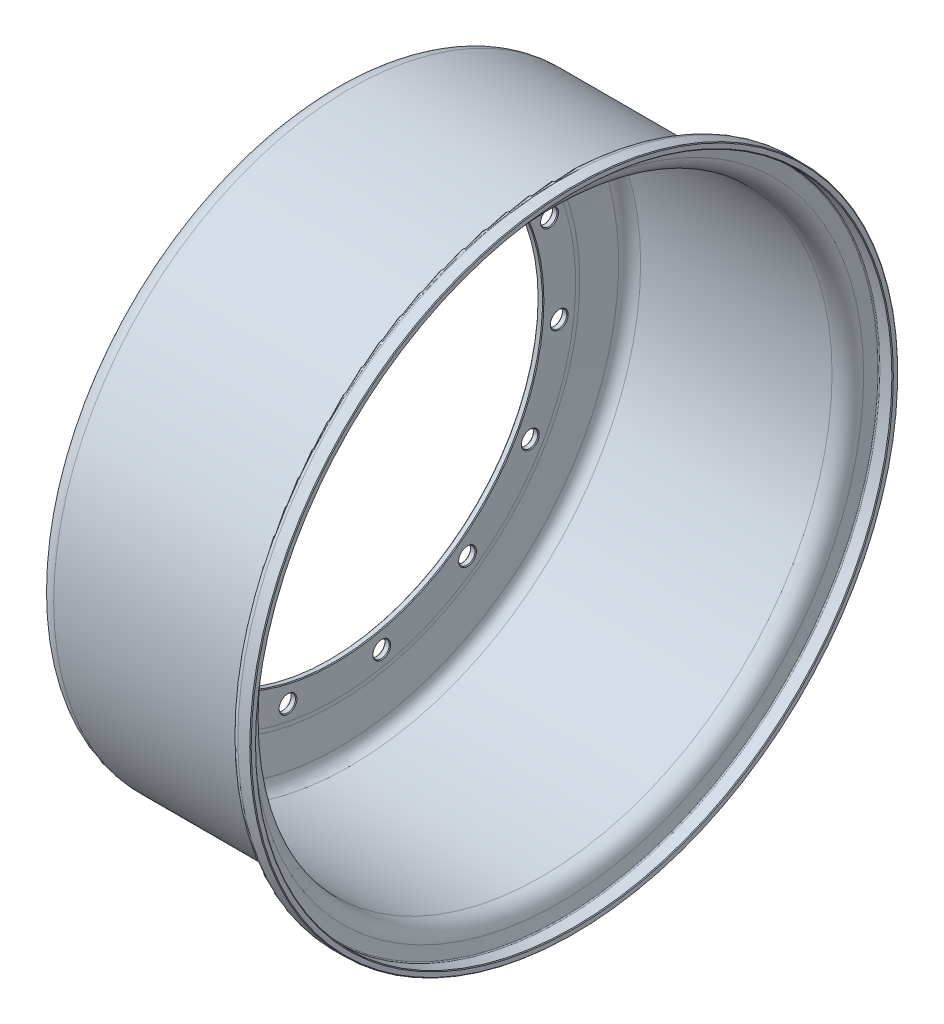
SolidWorks part; units mm, degrees
material "6061-T6 (SS)"
ref_plane "Front Plane" through (0, 0, 0) normal (0, 0, 1) x (1, 0, 0)
ref_plane "Top Plane" through (0, 0, 0) normal (0, 1, 0) x (1, 0, 0)
ref_plane "Right Plane" through (0, 0, 0) normal (1, 0, 0) x (0, 0, -1)
ref_axis "Axis1" through (-6.731, 0, 0) along (1, 0, 0)
sketch "Sketch1" plane through (0, 0, 0) normal (0, 0, 1) x (1, 0, 0)
  line L0 (0, -97.7897) -> (0, 97.7897) construction
  line L1 (0, 114.3) -> (0, 132.1206)
  line L2 (0.1187, 134.574) -> (2.0071, 154.0431)
  line L3 (3.175, 114.3) -> (3.175, 132.1206)
  line L4 (11.4879, 162.6489) -> (116.5449, 162.6489)
  line L5 (122.8075, 167.9487) -> (123.9262, 174.6196)
  line L6 (127.6838, 177.7995) -> (134.6206, 177.7995)
  line L7 (3.2789, 134.2674) -> (5.1673, 153.7366)
  line L8 (11.4879, 159.4739) -> (116.5449, 159.4739)
  line L9 (125.9388, 167.4236) -> (127.0575, 174.0945)
  line L10 (127.6838, 174.6245) -> (134.6206, 174.6245)
  line L11 (134.6206, 177.7995) -> (134.6206, 174.6245)
  line L12 (0, 114.3) -> (3.175, 114.3)
  arc A0 (0, 132.1206) -> (0.1187, 134.574) centre (25.4122, 132.1206) cw
  arc A1 (2.0071, 154.0431) -> (11.4879, 162.6489) centre (11.4879, 153.1235) cw
  arc A2 (116.5449, 162.6489) -> (122.8075, 167.9487) centre (116.5449, 168.999) ccw
  arc A3 (123.9262, 174.6196) -> (127.6838, 177.7995) centre (127.6838, 173.9894) cw
  arc A4 (3.175, 132.1206) -> (3.2789, 134.2674) centre (25.4122, 132.1206) cw
  arc A5 (5.1673, 153.7366) -> (11.4879, 159.4739) centre (11.4879, 153.1235) cw
  arc A6 (116.5449, 159.4739) -> (125.9388, 167.4236) centre (116.5449, 168.999) ccw
  arc A7 (127.0575, 174.0945) -> (127.6838, 174.6245) centre (127.6838, 173.9894) cw
  dimension "D4" = 2.4562
  dimension "D2" = 114.3
  dimension "D3" = 174.46
  dimension "D5" = 17.8206
  dimension "D6" = 19.5605
  dimension "D7" = 12.8041
  dimension "D8" = 105.0569
  dimension "D9" = 8.2042
  dimension "D10" = 6.764
  dimension "D11" = 99.52
  dimension "D12" = 4.9225
  dimension "D13" = 6.9367
  dimension "D14" = 3.175
revolve "Outer Rim" add sketch "Sketch1" angle 360 about axis through (-6.731, 0, 0) along (1, 0, 0)
sketch "Sketch2" plane through (0, 0, 0) normal (-1, 0, 0) x (0, 0, 1)
  circle A0 centre (0, 123.825) radius 4.4983
  circle A1 centre (0, 0) radius 114.3 construction
  dimension "D2" = 8.9967
  dimension "D1" = 9.525
extrude "Mounting Hole" cut sketch "Sketch2" against normal through all
pattern_circular "Mounting Hole Pattern" count 15 over 360 about axis through (0, 0, 0) along (1, 0, 0) of "Mounting Hole"
chamfer "Edge Chamfer" distance 0.3962 angle 45 34 edges at (3.175, 0, 114.3) (3.175, 123.825, 4.4983) (3.175, 113.1198, 54.8625) (3.175, 82.8551, 96.5182) (3.175, 38.264, 122.2629) (3.175, -12.9432, 127.645) (3.175, -61.9125, 111.7339) (3.175, -100.1765, 77.2808) (3.175, -121.1191, 30.243) (3.175, -121.1191, -21.2463) (3.175, -100.1765, -68.2842) (3.175, -61.9125, -102.7373) (3.175, -12.9432, -118.6483) (3.175, 38.264, -113.2662) (3.175, 82.8551, -87.5216) (3.175, 113.1198, -45.8658) (0, 0, 114.3) (0, 123.825, 4.4983) (0, 111.2901, 54.4736) (0, 79.5122, 95.0299) (0, 33.9859, 119.1546) (0, -17.4169, 122.6765) (0, -65.8082, 104.9864) (0, -102.8206, 69.1433) (0, -122.0544, 21.3446) (0, -120.1839, -30.1447) (0, -97.5325, -76.4217) (0, -58.0168, -109.4848) (0, -8.4695, -123.6169) (0, 42.5422, -116.3745) (0, 86.198, -89.0099) (0, 114.9494, -46.2547) (134.6206, 0, 174.6245) (134.6206, 0, 177.7995)
